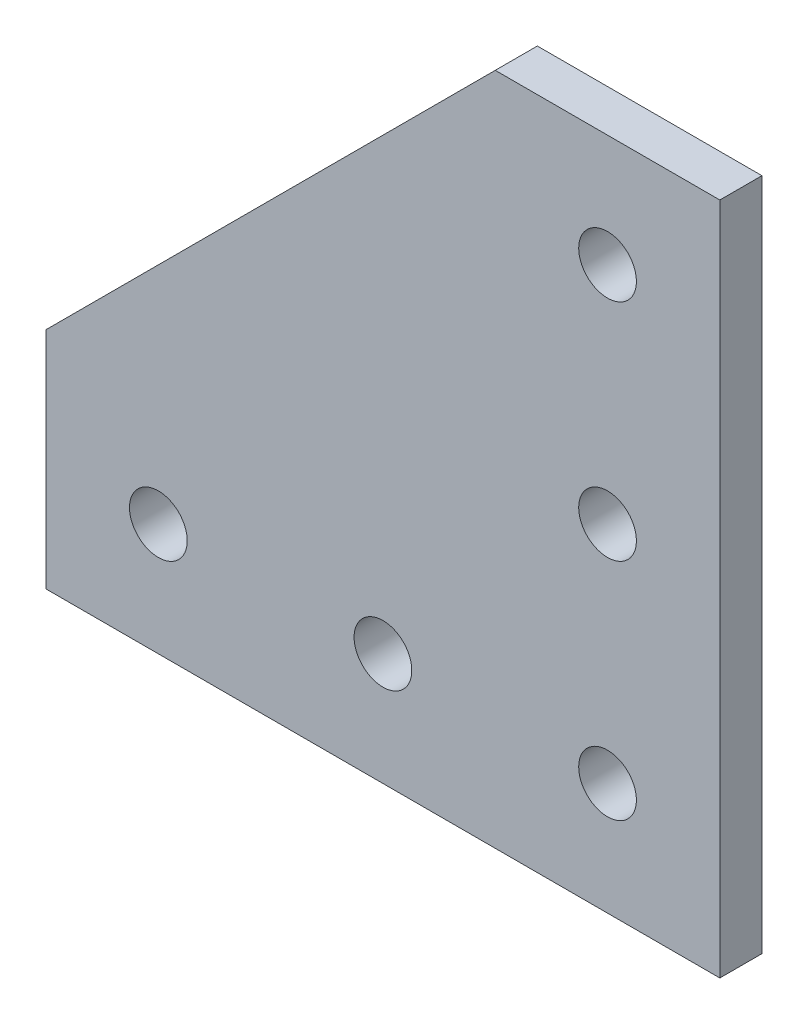
SolidWorks part; units mm, degrees
ref_plane "Front Plane" through (0, 0, 0) normal (0, 0, 1) x (1, 0, 0)
ref_plane "Top Plane" through (0, 0, 0) normal (0, 1, 0) x (1, 0, 0)
ref_plane "Right Plane" through (0, 0, 0) normal (1, 0, 0) x (0, 0, -1)
sketch "Sketch1" plane through (0, 0, 0) normal (0, 0, 1) x (1, 0, 0)
  line L0 (25.4, 25.4) -> (50.8, 25.4)
  line L1 (50.8, 25.4) -> (50.8, -50.8)
  line L2 (50.8, -50.8) -> (-25.4, -50.8)
  line L3 (-25.4, -50.8) -> (-25.4, -25.4)
  line L4 (-25.4, -25.4) -> (25.4, 25.4)
  dimension "D1" = 25.4
  dimension "height" = 76.2
  dimension "width" = 76.2
  dimension "flat" = 25.4
extrude "Extrude1" add sketch "Sketch1" against normal blind 4.7625
mirror "Mirror1" [suppressed]
sketch "Sketch2" plane through (0, 0, -4.7625) normal (0, 0, -1) x (-1, 0, 0)
  line L0 (-38.1, 25.4) -> (-38.1, -38.1) construction
  line L1 (-50.8, 25.4) -> (-25.4, 25.4) construction
  line L2 (25.4, -38.1) -> (-38.1, -38.1) construction
  line L3 (25.4, -25.4) -> (25.4, -50.8) construction
  circle A0 centre (-38.1, -38.1) radius 3.2639
  circle A1 centre (-12.7, -38.1) radius 3.2639
  circle A2 centre (12.7, -38.1) radius 3.2639
  circle A3 centre (-38.1, -12.7) radius 3.2639
  circle A4 centre (-38.1, 12.7) radius 3.2639
  dimension "hole" = 6.5278
  dimension "D2" = 25.4
  dimension "D3" = 25.4
  dimension "D4" = 25.4
  dimension "center to center" = 25.4
extrude "single 90" cut sketch "Sketch2" against normal through all
sketch "Sketch3" [suppressed] plane through (0, 0, -6.35) normal (0, 0, -1) x (-1, 0, 0)
  line L0 (-63.5, -38.1) -> (12.7, -38.1) construction
  line L1 (-63.5, -25.4) -> (-63.5, -50.8) construction
  line L2 (12.7, -25.4) -> (12.7, -50.8) construction
  line L3 (-25.4, 25.4) -> (-25.4, -38.1) construction
  line L4 (-38.1, 25.4) -> (-12.7, 25.4) construction
  circle A0 centre (-25.4, -38.1) radius 3.2639
  circle A1 centre (-25.4, -12.7) radius 3.2639
  circle A2 centre (-25.4, 12.7) radius 3.2639
  circle A3 centre (-50.8, -38.1) radius 3.2639
  circle A4 centre (0, -38.1) radius 3.2639
  dimension "D1" = 6.5278
  dimension "D3" = 25.4
  dimension "D4" = 25.4
  dimension "D5" = 25.4
  dimension "center to center" = 25.4
extrude "single tee" [suppressed] cut sketch "Sketch3" against normal through all
sketch "Sketch4" plane through (0, 0, -4.7625) normal (0, 0, -1) x (-1, 0, 0)
  line L0 (25.4, -50.8) -> (25.4, -38.1) construction
  line L1 (25.4, -25.4) -> (25.4, -50.8) construction
  line L2 (25.4, -38.1) -> (25.4, -25.4) construction
  line L3 (-50.8, 25.4) -> (-38.1, 25.4) construction
  line L4 (-50.8, 25.4) -> (-25.4, 25.4) construction
  line L5 (-38.1, 25.4) -> (-25.4, 25.4) construction
  line L6 (-44.45, 25.4) -> (-44.45, -44.45) construction
  line L7 (25.4, -44.45) -> (-44.45, -44.45) construction
  line L8 (25.4, -31.75) -> (-31.75, -31.75) construction
  line L9 (-31.75, 25.4) -> (-31.75, -31.75) construction
  circle A0 centre (-44.45, -44.45) radius 3.2639
  circle A1 centre (-31.75, -31.75) radius 3.2639
  circle A2 centre (-31.75, -44.45) radius 3.2639
  circle A3 centre (-44.45, -31.75) radius 3.2639
  circle A4 centre (-6.35, -31.75) radius 3.2639
  circle A5 centre (19.05, -31.75) radius 3.2639
  circle A6 centre (-6.35, -44.45) radius 3.2639
  circle A7 centre (19.05, -44.45) radius 3.2639
  circle A8 centre (-44.45, -6.35) radius 3.2639
  circle A9 centre (-44.45, 19.05) radius 3.2639
  circle A10 centre (-31.75, 19.05) radius 3.2639
  circle A11 centre (-31.75, -6.35) radius 3.2639
  dimension "D3" = 25.4
  dimension "D4" = 25.4
  dimension "D5" = 6.5278
  dimension "center to center" = 25.4
  dimension "D2" = 25.4
extrude "double 90" [suppressed] cut sketch "Sketch4" against normal through all
sketch "Sketch5" plane through (0, 0, -4.7625) normal (0, 0, -1) x (-1, 0, 0)
  line L0 (-38.1, 25.4) -> (-38.1, -50.8) construction
  line L1 (-50.8, 25.4) -> (-25.4, 25.4) construction
  line L2 (-38.1, 25.4) -> (-25.4, 25.4) construction
  line L3 (-31.75, 25.4) -> (-31.75, -44.45) construction
  line L4 (25.4, -50.8) -> (25.4, -38.1) construction
  line L5 (25.4, -25.4) -> (25.4, -50.8) construction
  line L6 (25.4, -38.1) -> (25.4, -25.4) construction
  line L7 (25.4, -31.75) -> (-31.75, -31.75) construction
  line L8 (25.4, -44.45) -> (-31.75, -44.45) construction
  line L9 (25.4, -50.8) -> (-50.8, -50.8) construction
  circle A0 centre (-31.75, -31.75) radius 3.2639
  circle A1 centre (-31.75, -44.45) radius 3.2639
  circle A2 centre (-6.35, -44.45) radius 3.2639
  circle A3 centre (-6.35, -31.75) radius 3.2639
  circle A4 centre (-31.75, -6.35) radius 3.2639
  circle A5 centre (-31.75, 19.05) radius 3.2639
  circle A6 centre (-44.45, -44.45) radius 3.2639
  circle A7 centre (-69.85, -44.45) radius 3.2639
  circle A8 centre (-69.85, -31.75) radius 3.2639
  circle A9 centre (-44.45, -31.75) radius 3.2639
  circle A10 centre (-44.45, -6.35) radius 3.2639
  circle A11 centre (-44.45, 19.05) radius 3.2639
  dimension "D2" = 25.4
  dimension "D3" = 25.4
  dimension "D1" = 6.5278
  dimension "center to center" = 25.4
extrude "double tee" [suppressed] cut sketch "Sketch5" against normal through all
equation "\"D2@Sketch2\" = \"center to center@Sketch2\""
equation "\"D3@Sketch2\" = \"center to center@Sketch2\""
equation "\"D4@Sketch2\" = \"center to center@Sketch2\""
equation "\"D1@Sketch3\" = \"hole@Sketch2\""
equation "\"D5@Sketch3\" = \"center to center@Sketch3\""
equation "\"D3@Sketch3\" = \"center to center@Sketch3\""
equation "\"D4@Sketch3\" = \"center to center@Sketch3\""
equation "\"D2@Sketch4\" = \"center to center@Sketch4\""
equation "\"D3@Sketch4\" = \"center to center@Sketch4\""
equation "\"D4@Sketch4\" = \"center to center@Sketch4\""
equation "\"D5@Sketch4\" = \"hole@Sketch2\""
equation "\"D1@Sketch5\" = \"hole@Sketch2\""
equation "\"D2@Sketch5\" = \"center to center@Sketch5\""
equation "\"D3@Sketch5\" = \"center to center@Sketch5\""
